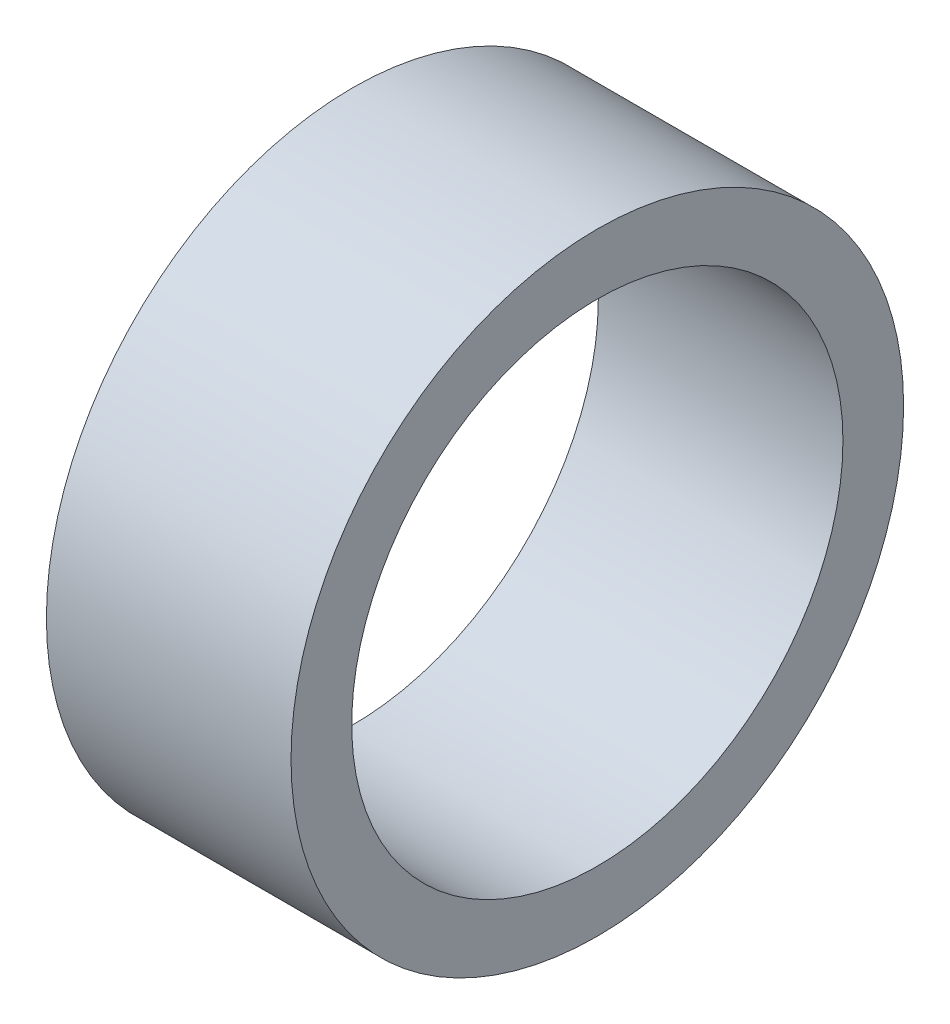
SolidWorks part; units mm, degrees
material "6061-T6 (SS)"
ref_plane "Front" through (0, 0, 0) normal (0, 0, 1) x (1, 0, 0)
ref_plane "Top" through (0, 0, 0) normal (0, 1, 0) x (1, 0, 0)
ref_plane "Right" through (0, 0, 0) normal (1, 0, 0) x (0, 0, -1)
sketch "Sketch1" plane through (0, 0, 0) normal (1, 0, 0) x (0, 0, -1)
  circle A0 centre (0, 0) radius 3.1877
  circle A1 centre (0, 0) radius 3.9751
  dimension "D1" = 6.3754
  dimension "D2" = 7.9502
extrude "Boss-Extrude1" add sketch "Sketch1" along normal mid plane 3.175
